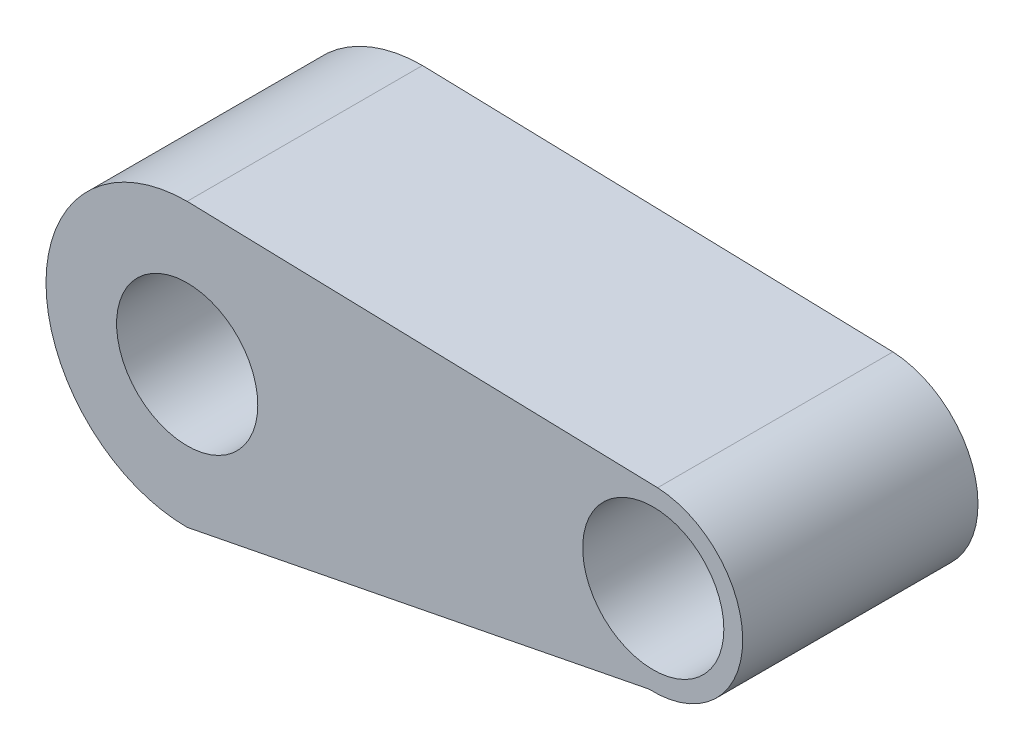
SolidWorks part; units mm, degrees
ref_plane "Front Plane" through (0, 0, 0) normal (0, 0, 1) x (1, 0, 0)
ref_plane "Top Plane" through (0, 0, 0) normal (0, 1, 0) x (1, 0, 0)
ref_plane "Right Plane" through (0, 0, 0) normal (1, 0, 0) x (0, 0, -1)
sketch "Sketch1" plane through (0, 0, 0) normal (0, 0, 1) x (1, 0, 0)
  line L2 (0, 3) -> (9.9963, 2.7276)
  line L3 (0, -3) -> (9.8119, -1.0698)
  circle A0 centre (0, 0) radius 1.5
  circle A1 centre (0, 0) radius 3
  arc A2 (9.9963, 2.7276) -> (9.8119, -1.0698) centre (9.9041, 0.8289) cw
  circle A3 centre (9.9041, 0.8289) radius 1.5
  dimension "D1" = 3
  dimension "D2" = 6
  dimension "D3" = 3
  dimension "D4" = 10
  dimension "D5" = 10
extrude "Boss-Extrude1" add sketch "Sketch1" along normal blind 5 contours L2 A1 L3 A0 | A2 L2 A1 L3
